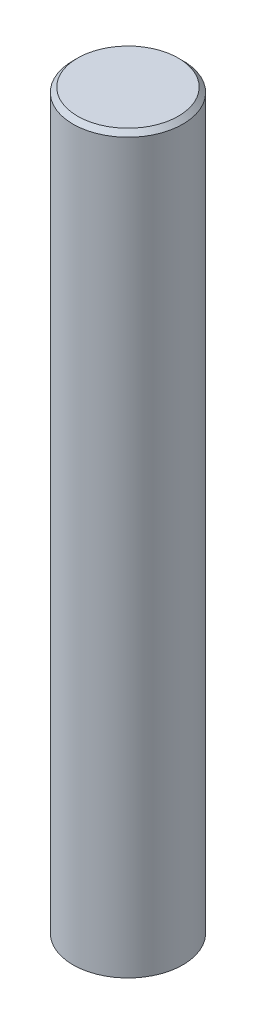
SolidWorks part; units mm, degrees
ref_plane "Front Plane" through (0, 0, 0) normal (0, 0, 1) x (1, 0, 0)
ref_plane "Top Plane" through (0, 0, 0) normal (0, 1, 0) x (1, 0, 0)
ref_plane "Right Plane" through (0, 0, 0) normal (1, 0, 0) x (0, 0, -1)
sketch "Sketch1" plane through (0, 0, 0) normal (0, 1, 0) x (1, 0, 0)
  circle A0 centre (0, 0) radius 12
  dimension "D1" = 24
extrude "Boss-Extrude1" add sketch "Sketch1" along normal blind 160
chamfer "Chamfer1" distance 1 angle 45 1 edges at (0, 160, 12)
